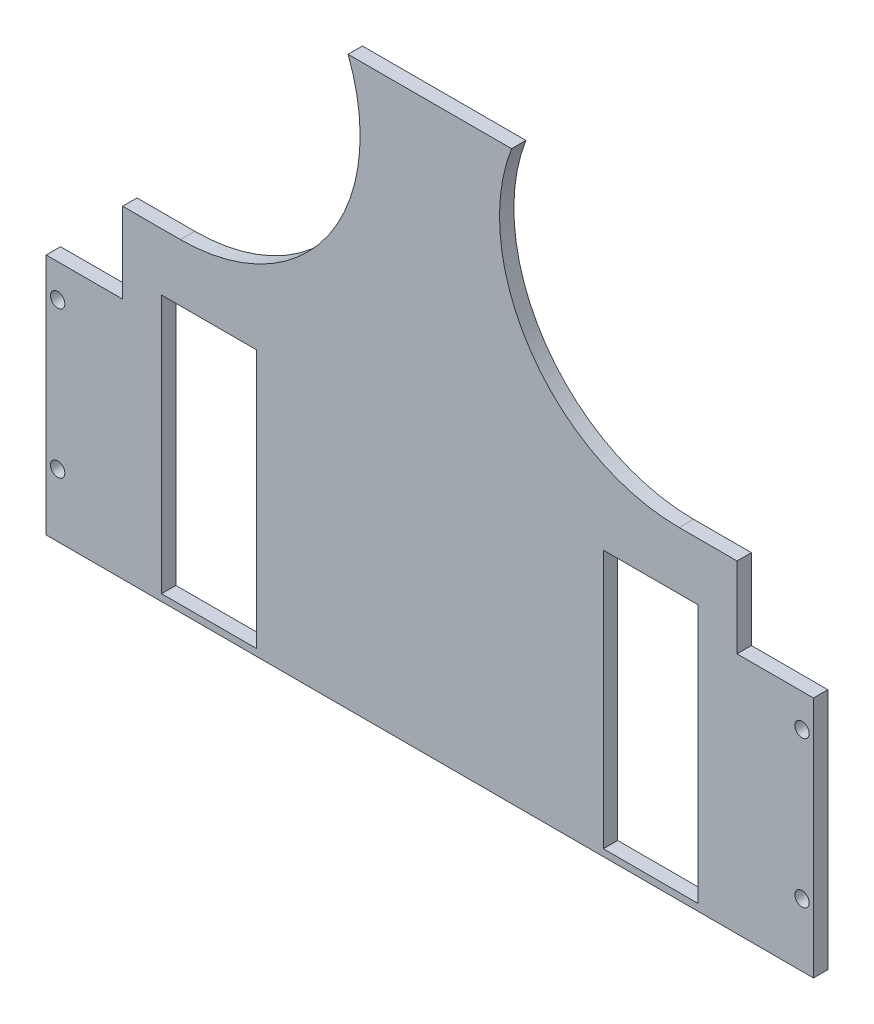
SolidWorks part; units mm, degrees
ref_plane "Front Plane" through (0, 0, 0) normal (0, 0, 1) x (1, 0, 0)
ref_plane "Top Plane" through (0, 0, 0) normal (0, 1, 0) x (1, 0, 0)
ref_plane "Right Plane" through (0, 0, 0) normal (1, 0, 0) x (0, 0, -1)
sketch "Sketch1" plane through (0, 0, 0) normal (0, 0, 1) x (1, 0, 0)
  line L0 (-3262.1, -69) -> (-3262.1, -336.4) construction
  line L1 (-3395.6, -69) -> (-3128.6, -69)
  line L2 (-3395.6, -69) -> (-3395.6, -336.4)
  line L3 (-3395.6, -336.4) -> (-3128.6, -336.4)
  line L4 (-3128.6, -69) -> (-3128.6, -336.4)
  line L9 (-3201.74, -174) -> (-3168.74, -174)
  line L10 (-3201.74, -174) -> (-3201.74, -264)
  line L11 (-3201.74, -264) -> (-3168.74, -264)
  line L12 (-3168.74, -174) -> (-3168.74, -264)
  line L13 (-3237.8504, -69) -> (-3286.3496, -69) construction
  line L14 (-3355.46, -219) -> (-3168.74, -219) construction
  line L15 (-3128.6, -336.4) -> (-3128.6, -182) construction
  line L21 (-3395.6, -182) -> (-3395.6, -336.4) construction
  line L25 (-3128.6, -336.4) -> (-3199.6, -336.4) construction
  line L52 (-3182.74, -174) -> (-3182.74, -264) construction
  line L53 (-3192.74, -174) -> (-3172.74, -174) construction
  line L54 (-3192.74, -174) -> (-3192.74, -264) construction
  line L55 (-3192.74, -264) -> (-3172.74, -264) construction
  line L56 (-3172.74, -174) -> (-3172.74, -264) construction
  line L102 (-3132.6, -193.5) -> (-3132.6, -244.5) construction
  line L103 (-3168.74, -219) -> (-3132.6, -219) construction
  line L134 (-3355.46, -219) -> (-3391.6, -219) construction
  line L135 (-3391.6, -193.5) -> (-3391.6, -244.5) construction
  line L139 (-3351.46, -174) -> (-3351.46, -264) construction
  line L140 (-3331.46, -264) -> (-3351.46, -264) construction
  line L141 (-3331.46, -174) -> (-3331.46, -264) construction
  line L142 (-3331.46, -174) -> (-3351.46, -174) construction
  line L143 (-3341.46, -174) -> (-3341.46, -264) construction
  line L154 (-3355.46, -174) -> (-3355.46, -264)
  line L155 (-3322.46, -264) -> (-3355.46, -264)
  line L156 (-3322.46, -174) -> (-3322.46, -264)
  line L157 (-3322.46, -174) -> (-3355.46, -174)
  circle A84 centre (-3132.6, -193.5) radius 2.5
  circle A85 centre (-3132.6, -244.5) radius 2.5
  circle A236 centre (-3391.6, -244.5) radius 2.5
  circle A237 centre (-3391.6, -193.5) radius 2.5
  dimension "D5" = 20
  dimension "D15" = 5
  dimension "D16" = 5
  dimension "D2" = 105
  dimension "D3" = 4
  dimension "D4" = 90
  dimension "D6" = 90
  dimension "D7" = 9
  dimension "D14" = 89.36
  dimension "D17" = 25.5
  dimension "D18" = 4
extrude "Boss-Extrude1" add sketch "Sketch1" along normal blind 5
ref_plane "Plane1"
sketch "Sketch6" plane through (0, 0, 5) normal (0, 0, 1) x (1, 0, 0)
  line L13 (-3128.6, -336.4) -> (-3128.6, -69) construction
  line L17 (-3233.6599, -69) -> (-3128.6, -69)
  line L19 (-3368.9957, -154) -> (-3348.8496, -154) construction
  line L24 (-3395.6, -336.4) -> (-3128.6, -336.4)
  line L26 (-3395.6, -336.4) -> (-3395.6, -266.3756)
  line L27 (-3128.6, -336.4) -> (-3128.6, -266.3756)
  line L28 (-3395.6, -266.3756) -> (-3128.6, -266.3756)
  line L30 (-3128.6, -69) -> (-3395.6, -69) construction
  line L32 (-3128.6, -69) -> (-3128.6, -182)
  line L33 (-3128.6, -336.4) -> (-3128.6, -69) construction
  line L34 (-3128.6, -182) -> (-3155.2043, -182)
  line L35 (-3155.2043, -182) -> (-3155.2043, -154)
  line L36 (-3155.2043, -154) -> (-3175.3504, -154)
  line L37 (-3175.3504, -154) -> (-3145.95, -154) construction
  line L38 (-3290.5401, -69) -> (-3395.6, -69)
  line L39 (-3395.6, -69) -> (-3395.6, -182)
  line L40 (-3395.6, -69) -> (-3395.6, -336.4) construction
  line L41 (-3395.6, -182) -> (-3368.9957, -182)
  line L42 (-3368.9957, -182) -> (-3368.9957, -154)
  line L44 (-3368.9957, -182) -> (-3368.9957, -154) construction
  line L45 (-3368.9957, -154) -> (-3348.8496, -154)
  arc A4 (-3348.8496, -154) -> (-3286.3496, -91.5) centre (-3348.8496, -91.5) ccw construction
  arc A5 (-3233.6599, -69) -> (-3175.3504, -154) centre (-3175.3504, -91.5) ccw construction
  arc A6 (-3175.3504, -154) -> (-3233.6599, -69) centre (-3175.3504, -91.5) cw
  arc A7 (-3348.8496, -154) -> (-3290.5401, -69) centre (-3348.8496, -91.5) ccw
  dimension "D1" = 62.5
extrude "Cut-Extrude4" cut sketch "Sketch6" against normal through all
